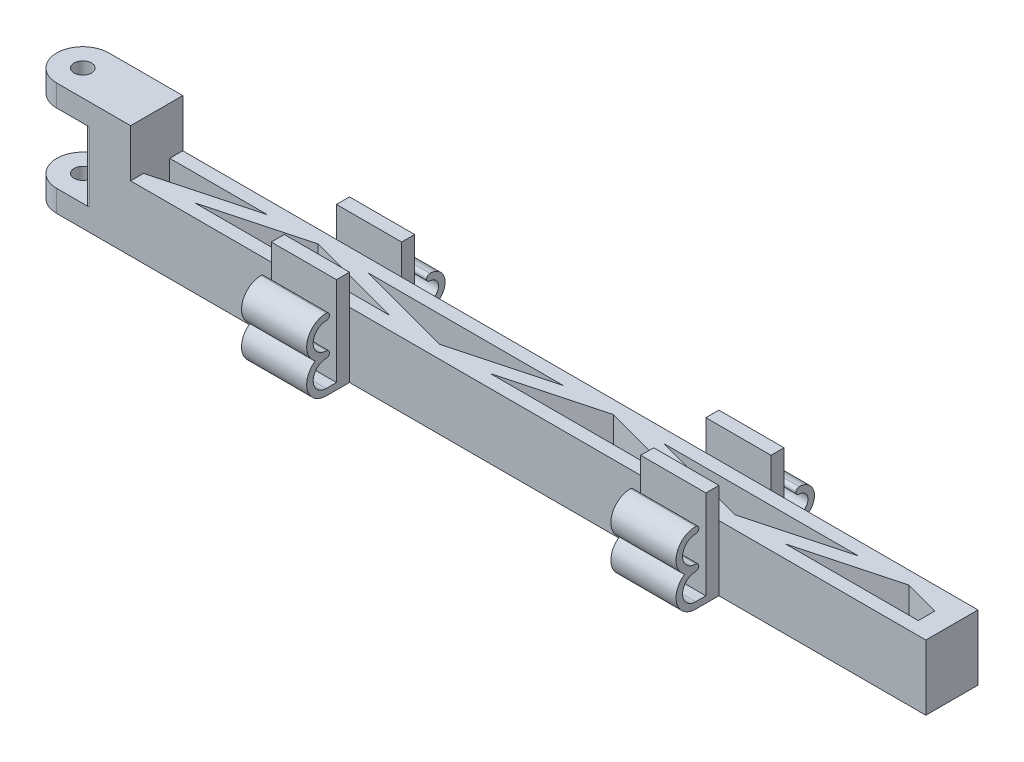
SolidWorks part; units mm, degrees
ref_plane "Front Plane" through (0, 0, 0) normal (0, 0, 1) x (1, 0, 0)
ref_plane "Top Plane" through (0, 0, 0) normal (0, 1, 0) x (1, 0, 0)
ref_plane "Right Plane" through (0, 0, 0) normal (1, 0, 0) x (0, 0, -1)
sketch "Sketch1" plane through (0, 0, 0) normal (0, 1, 0) x (1, 0, 0)
  line L0 (200, -6) -> (200, 6)
  line L1 (200, 6) -> (0, 6)
  line L2 (200, -6) -> (0, -6)
  line L3 (-5.2163, 3) -> (-5.1962, 3)
  line L6 (17.176, -3) -> (39.5684, 3)
  line L7 (0, 0) -> (2, 0) construction
  line L8 (28.7672, -3) -> (51.1595, 3)
  line L9 (17.176, -3) -> (5.9799, 0)
  line L10 (51.1595, 3) -> (73.5518, -3)
  line L11 (62.7506, 3) -> (85.1429, -3)
  line L12 (195.2574, -3) -> (195.2574, 0.8124)
  line L13 (85.1429, -3) -> (107.5352, 3)
  line L14 (96.734, -3) -> (119.1263, 3)
  line L15 (119.1263, 3) -> (141.5186, -3)
  line L16 (130.7174, 3) -> (153.1097, -3)
  line L17 (153.1097, -3) -> (175.502, 3)
  line L18 (164.7008, -3) -> (187.0931, 3)
  line L19 (187.0931, 3) -> (195.2574, 0.8124)
  line L27 (175.897, 0) -> (195.2574, 0) construction
  line L28 (164.7008, -3) -> (195.2574, -3)
  line L29 (130.7174, 3) -> (175.502, 3)
  line L30 (141.9136, 0) -> (164.3059, 0) construction
  line L31 (107.9301, 0) -> (130.3224, 0) construction
  line L32 (96.734, -3) -> (141.5186, -3)
  line L33 (73.9467, 0) -> (96.339, 0) construction
  line L34 (62.7506, 3) -> (107.5352, 3)
  line L35 (39.9633, 0) -> (62.3556, 0) construction
  line L36 (28.7672, -3) -> (73.5518, -3)
  line L37 (5.9799, 0) -> (28.3722, 0) construction
  line L39 (5.1962, 3) -> (39.5684, 3)
  line L40 (-5.1988, 2.9953) -> (-5.2163, 3)
  circle A0 centre (0, 0) radius 2
  arc A1 (0, 6) -> (0, -6) centre (0, 0) ccw
  arc A3 (0, 6) -> (0, -6) centre (0, 0) ccw
  arc A6 (0, 6) -> (0, -6) centre (0, 0) ccw
  arc A7 (6, -0.0054) -> (6, 0) centre (0, 0) ccw
  arc A8 (6, -0.0054) -> (5.1962, 3) centre (0, 0) ccw
  arc A9 (6, -0.0054) -> (5.1962, 3) centre (0, 0) ccw
  point P6 (200, 0)
  dimension "D1" = 4
  dimension "D4" = 12
  dimension "D2" = 12
  dimension "D3" = 200
  dimension "D5" = 3
  dimension "D8" = 165
  dimension "D9" = 165
  dimension "D10" = 3
  dimension "D11" = 3
  dimension "D13" = 3
  dimension "D14" = 3
  dimension "D15" = 3
  dimension "D18" = 6
  dimension "D19" = 6
  dimension "D20" = 6
  dimension "D21" = 6
  dimension "D22" = 6
  dimension "D23" = 6
extrude "Boss-Extrude1" add sketch "Sketch1" along normal blind 15
sketch "Sketch2" plane through (0, 15, 0) normal (0, 1, 0) x (1, 0, 0)
  line L0 (200, -6) -> (0, -6) construction
  line L1 (0, 6) -> (17, 6)
  line L2 (0, 6) -> (0, 2)
  line L3 (0, -6) -> (17, -6)
  line L4 (17, 6) -> (17, -6)
  circle A0 centre (0, 0) radius 2
  arc A1 (0, 6) -> (0, -6) centre (0, 0) ccw
  dimension "D1" = 17
extrude "Boss-Extrude2" add sketch "Sketch2" along normal blind 5
sketch "Sketch3" plane through (0, 0, 0) normal (0, -1, 0) x (1, 0, 0)
  circle A1 centre (0, 0) radius 8
  dimension "D1" = 16
extrude "Cut-Extrude1" cut sketch "Sketch3" against normal up to surface (15 mm away) up to face at (11.3486, 15, -0.7737)
sketch "Sketch4" plane through (0, 15, 0) normal (0, -1, 0) x (1, 0, 0)
  line L5 (7.4162, -3) -> (17, -3)
  line L6 (17, -3) -> (17, 2.9528)
  line L7 (17, 2.9528) -> (7.982, 0.5365)
  line L8 (5.2915, 6) -> (0, 6)
  line L9 (0, -6) -> (5.2915, -6)
  line L10 (7.4162, -3) -> (17, -3)
  line L11 (17, -3) -> (17, 2.9528)
  line L12 (17, 2.9528) -> (7.982, 0.5365)
  arc A0 (7.982, 0.5365) -> (7.4162, -3) centre (0, 0) cw
  arc A3 (5.2915, -6) -> (7.4162, -3) centre (0, 0) ccw
  arc A4 (7.982, 0.5365) -> (5.2915, 6) centre (0, 0) ccw
  arc A5 (0, 6) -> (0, -6) centre (0, 0) ccw
  dimension "D1" = 0
extrude "Boss-Extrude3" add sketch "Sketch4" along normal up to surface (15 mm away) up to face at (85.1429, 0, -1)
sketch "Sketch5" plane through (0, 0, 0) normal (0, -1, 0) x (1, 0, 0)
  line L3 (17, -6) -> (17, 6)
  line L4 (0, -6) -> (17, -6)
  line L5 (17, 6) -> (0, 6)
  line L6 (17, -6) -> (17, 6)
  line L7 (0, -6) -> (17, -6)
  line L8 (17, 6) -> (0, 6)
  circle A0 centre (0, 0) radius 2
  arc A1 (0, 6) -> (0, -6) centre (0, 0) ccw
  arc A2 (0, 6) -> (0, -6) centre (0, 0) ccw
  dimension "D1" = 0
extrude "Boss-Extrude4" add sketch "Sketch5" against normal blind 5
fillet "Fillet4" radius 1 2 edges at (5.2915, 10, -6) (5.2915, 10, 6)
sketch "Sketch11" plane through (0, 0, 0) normal (0, -1, 0) x (1, 0, 0)
  line L0 (200, 6) -> (0, 6) construction
  line L1 (52.3705, 6) -> (67.3705, 6)
  line L2 (52.3705, 6) -> (52.3705, 9)
  line L3 (52.3705, 9) -> (67.3705, 9)
  line L4 (67.3705, 6) -> (67.3705, 9)
  line L5 (200, -6) -> (0, -6) construction
  line L6 (52.3705, -6) -> (67.3705, -6)
  line L7 (52.3705, -6) -> (52.3705, -9)
  line L8 (52.3705, -9) -> (67.3705, -9)
  line L9 (67.3705, -6) -> (67.3705, -9)
  line L11 (137.3705, 6) -> (152.3705, 6)
  line L12 (137.3705, 6) -> (137.3705, 9)
  line L13 (137.3705, 9) -> (152.3705, 9)
  line L14 (152.3705, 6) -> (152.3705, 9)
  line L15 (137.3705, -6) -> (152.3705, -6)
  line L16 (137.3705, -6) -> (137.3705, -9)
  line L17 (137.3705, -9) -> (152.3705, -9)
  line L18 (152.3705, -6) -> (152.3705, -9)
  dimension "D1" = 3
  dimension "D2" = 15
  dimension "D3" = 70
extrude "Boss-Extrude6" add sketch "Sketch11" against normal blind 22
sketch "Sketch12" plane through (0, 15, 0) normal (0, -1, 0) x (1, 0, 0)
  line L2 (0, -6) -> (7.4833, -6)
  line L3 (7.4833, 6) -> (0, 6)
  line L4 (0, -6) -> (7.4833, -6)
  line L5 (7.4833, 6) -> (0, 6)
  arc A4 (6.6518, -4.4444) -> (7.4833, -6) centre (7.4833, -5) ccw
  arc A5 (6.6518, -4.4444) -> (6.6518, 4.4444) centre (0, 0) ccw
  arc A6 (7.4833, 6) -> (6.6518, 4.4444) centre (7.4833, 5) ccw
  arc A7 (0, 6) -> (0, -6) centre (0, 0) ccw
  arc A8 (6.6518, -4.4444) -> (7.4833, -6) centre (7.4833, -5) ccw
  arc A9 (6.6518, -4.4444) -> (6.6518, 4.4444) centre (0, 0) ccw
  arc A10 (7.4833, 6) -> (6.6518, 4.4444) centre (7.4833, 5) ccw
  arc A11 (0, 6) -> (0, -6) centre (0, 0) ccw
  dimension "D1" = 0
extrude "Cut-Extrude4" cut sketch "Sketch12" against normal through all
sketch "Sketch13" plane through (0, 20, 0) normal (0, 1, 0) x (1, 0, 0)
  line L3 (7.4833, -6) -> (17, -6)
  line L4 (17, -6) -> (17, 6)
  line L5 (17, 6) -> (7.4833, 6)
  line L6 (7.4833, -6) -> (17, -6)
  line L7 (17, -6) -> (17, 6)
  line L8 (17, 6) -> (7.4833, 6)
  arc A3 (6.6518, -4.4444) -> (7.4833, -6) centre (7.4833, -5) ccw
  arc A4 (7.4833, 6) -> (6.6518, 4.4444) centre (7.4833, 5) ccw
  arc A5 (6.6518, -4.4444) -> (6.6518, 4.4444) centre (0, 0) ccw
  arc A6 (6.6518, -4.4444) -> (7.4833, -6) centre (7.4833, -5) ccw
  arc A7 (7.4833, 6) -> (6.6518, 4.4444) centre (7.4833, 5) ccw
  arc A8 (6.6518, -4.4444) -> (6.6518, 4.4444) centre (0, 0) ccw
  dimension "D1" = 0
extrude "Boss-Extrude7" add sketch "Sketch13" along normal blind 1
sketch "Sketch14" plane through (0, 21, 0) normal (0, 1, 0) x (1, 0, 0)
  line L2 (0, -6) -> (7.4833, -6)
  line L3 (7.4833, 6) -> (0, 6)
  line L4 (0, -6) -> (7.4833, -6)
  line L5 (7.4833, 6) -> (0, 6)
  line L7 (7.4833, -6) -> (17, -6)
  line L8 (17, -6) -> (17, 6)
  line L9 (17, 6) -> (7.4833, 6)
  line L10 (7.4833, -6) -> (17, -6)
  line L11 (17, -6) -> (17, 6)
  line L12 (17, 6) -> (7.4833, 6)
  circle A0 centre (0, 0) radius 2 construction
  circle A1 centre (0, 0) radius 2
  arc A3 (6.6518, -4.4444) -> (6.6518, 4.4444) centre (0, 0) ccw
  arc A4 (6.6518, -4.4444) -> (7.4833, -6) centre (7.4833, -5) ccw
  arc A5 (6.6518, -4.4444) -> (6.6518, 4.4444) centre (0, 0) ccw
  arc A6 (7.4833, 6) -> (6.6518, 4.4444) centre (7.4833, 5) ccw
  arc A7 (0, 6) -> (0, -6) centre (0, 0) ccw
  arc A11 (0, 6) -> (0, -6) centre (0, 0) ccw
  arc A12 (6.6518, -4.4444) -> (7.4833, -6) centre (7.4833, -5) ccw
  arc A13 (7.4833, 6) -> (6.6518, 4.4444) centre (7.4833, 5) ccw
  dimension "D1" = 0
  dimension "D2" = 0
extrude "Boss-Extrude8" add sketch "Sketch14" along normal blind 5
sketch "Sketch17" plane through (52.3705, 0, 0) normal (-1, 0, 0) x (0, 0, 1)
  line L2 (0, 26) -> (0, 0) construction
  line L3 (6, 26) -> (-6, 26) construction
  line L4 (-12.5, 1.5) -> (-9, 1.5)
  line L5 (-9, 1.5) -> (-9, 0)
  line L9 (-9, 0) -> (-12.5, 0)
  arc A0 (-12.5, 0) -> (-14.6651, 6.25) centre (-12.5, 3.5) cw
  arc A1 (-14.6651, 6.25) -> (-12.5, 12.5) centre (-12.5, 9) cw
  arc A2 (-12.5, 12.5) -> (-12.5, 11) centre (-12.5, 11.75) cw
  arc A3 (-12.5, 7) -> (-12.5, 11) centre (-12.5, 9) cw
  arc A4 (-12.5, 7) -> (-12.5, 5.5) centre (-12.5, 6.25) cw
  arc A5 (-12.5, 1.5) -> (-12.5, 5.5) centre (-12.5, 3.5) cw
extrude "Boss-Extrude9" add sketch "Sketch17" against normal up to surface (15 mm away) up to face at (67.3705, 11.8, 7.2)
sketch "Sketch18" plane through (152.3705, 0, 0) normal (1, 0, 0) x (0, 0, -1)
  line L6 (6, 0) -> (12.5, 0)
  line L7 (12.5, 1.5) -> (9, 1.5)
  line L8 (9, 1.5) -> (9, 22)
  line L9 (9, 22) -> (6, 22)
  line L10 (6, 22) -> (6, 15)
  line L11 (6, 15) -> (6, 0)
  line L12 (6, 0) -> (12.5, 0)
  line L13 (12.5, 1.5) -> (9, 1.5)
  line L14 (9, 1.5) -> (9, 22)
  line L15 (9, 22) -> (6, 22)
  line L16 (6, 22) -> (6, 15)
  line L17 (6, 15) -> (6, 0)
  arc A6 (12.5, 0) -> (14.6651, 6.25) centre (12.5, 3.5) ccw
  arc A7 (14.6651, 6.25) -> (12.5, 12.5) centre (12.5, 9) ccw
  arc A8 (12.5, 12.5) -> (12.5, 11) centre (12.5, 11.75) ccw
  arc A9 (12.5, 7) -> (12.5, 11) centre (12.5, 9) ccw
  arc A10 (12.5, 7) -> (12.5, 5.5) centre (12.5, 6.25) ccw
  arc A11 (12.5, 1.5) -> (12.5, 5.5) centre (12.5, 3.5) ccw
  arc A12 (12.5, 0) -> (14.6651, 6.25) centre (12.5, 3.5) ccw
  arc A13 (14.6651, 6.25) -> (12.5, 12.5) centre (12.5, 9) ccw
  arc A14 (12.5, 12.5) -> (12.5, 11) centre (12.5, 11.75) ccw
  arc A15 (12.5, 7) -> (12.5, 11) centre (12.5, 9) ccw
  arc A16 (12.5, 7) -> (12.5, 5.5) centre (12.5, 6.25) ccw
  arc A17 (12.5, 1.5) -> (12.5, 5.5) centre (12.5, 3.5) ccw
  dimension "D1" = 0
extrude "Boss-Extrude10" add sketch "Sketch18" against normal up to surface (15 mm away) up to face at (137.3705, 11.8, -7.2)
ref_plane "Plane1" through (152.3705, 15, 6) normal (0, -1, 0) x (-1, 0, 0)
sketch "Sketch20" plane through (152.3705, 0, 0) normal (1, 0, 0) x (0, 0, -1)
  line L0 (-9, 22) -> (-9, 0) construction
  line L1 (-6, 0) -> (-9, 0) construction
  line L6 (-11.3648, 0) -> (-9, 0)
  line L7 (-9, 0) -> (-9, 1.5)
  line L8 (-9, 1.5) -> (-11.3648, 1.5)
  ellipse E12 centre (-11.3648, 12) end of major axis (-11.3648, 16.5) minor radius 4.4905 (-11.3648, 16.5) -> (-13.847, 8.25) ccw
  ellipse E13 centre (-11.3648, 4.5) end of major axis (-11.3648, 9) minor radius 4.4905 (-13.847, 8.25) -> (-11.3648, 0) ccw
  ellipse E14 centre (-11.3648, 4.5) end of major axis (-11.3648, 7.5) minor radius 2.9937 (-11.3648, 7.5) -> (-11.3648, 1.5) ccw
  ellipse E15 centre (-11.3648, 8.25) end of major axis (-11.3648, 9) minor radius 0.7484 (-11.3648, 7.5) -> (-11.3648, 9) ccw
  ellipse E16 centre (-11.3648, 12) end of major axis (-11.3648, 15) minor radius 2.9937 (-11.3648, 15) -> (-11.3648, 9) ccw
  ellipse E17 centre (-11.3648, 15.75) end of major axis (-11.3648, 16.5) minor radius 0.7484 (-11.3648, 15) -> (-11.3648, 16.5) ccw
extrude "Boss-Extrude11" add sketch "Sketch20" against normal up to surface (15 mm away) up to face at (137.3705, 11.8, 7.2)
sketch "Sketch21" plane through (52.3705, 0, 0) normal (-1, 0, 0) x (0, 0, 1)
  line L6 (6, 0) -> (11.3648, 0)
  line L7 (11.3648, 1.5) -> (9, 1.5)
  line L8 (9, 1.5) -> (9, 22)
  line L9 (9, 22) -> (6, 22)
  line L10 (6, 22) -> (6, 15)
  line L11 (6, 15) -> (6, 0)
  line L12 (6, 0) -> (11.3648, 0)
  line L13 (11.3648, 1.5) -> (9, 1.5)
  line L14 (9, 1.5) -> (9, 22)
  line L15 (9, 22) -> (6, 22)
  line L16 (6, 22) -> (6, 15)
  line L17 (6, 15) -> (6, 0)
  ellipse E6 centre (11.3648, 4.5) end of major axis (11.3648, 9) minor radius 4.4905 (11.3648, 0) -> (13.847, 8.25) ccw
  ellipse E7 centre (11.3648, 12) end of major axis (11.3648, 16.5) minor radius 4.4905 (13.847, 8.25) -> (11.3648, 16.5) ccw
  ellipse E8 centre (11.3648, 15.75) end of major axis (11.3648, 16.5) minor radius 0.7484 (11.3648, 16.5) -> (11.3648, 15) ccw
  ellipse E9 centre (11.3648, 12) end of major axis (11.3648, 15) minor radius 2.9937 (11.3648, 9) -> (11.3648, 15) ccw
  ellipse E10 centre (11.3648, 8.25) end of major axis (11.3648, 9) minor radius 0.7484 (11.3648, 9) -> (11.3648, 7.5) ccw
  ellipse E11 centre (11.3648, 4.5) end of major axis (11.3648, 7.5) minor radius 2.9937 (11.3648, 1.5) -> (11.3648, 7.5) ccw
  ellipse E12 centre (11.3648, 4.5) end of major axis (11.3648, 9) minor radius 4.4905 (11.3648, 0) -> (13.847, 8.25) ccw
  ellipse E13 centre (11.3648, 12) end of major axis (11.3648, 16.5) minor radius 4.4905 (13.847, 8.25) -> (11.3648, 16.5) ccw
  ellipse E14 centre (11.3648, 15.75) end of major axis (11.3648, 16.5) minor radius 0.7484 (11.3648, 16.5) -> (11.3648, 15) ccw
  ellipse E15 centre (11.3648, 12) end of major axis (11.3648, 15) minor radius 2.9937 (11.3648, 9) -> (11.3648, 15) ccw
  ellipse E16 centre (11.3648, 8.25) end of major axis (11.3648, 9) minor radius 0.7484 (11.3648, 9) -> (11.3648, 7.5) ccw
  ellipse E17 centre (11.3648, 4.5) end of major axis (11.3648, 7.5) minor radius 2.9937 (11.3648, 1.5) -> (11.3648, 7.5) ccw
  dimension "D1" = 0
extrude "Boss-Extrude12" add sketch "Sketch21" against normal up to surface (15 mm away) up to face at (67.3705, 11.8, 7.2)
